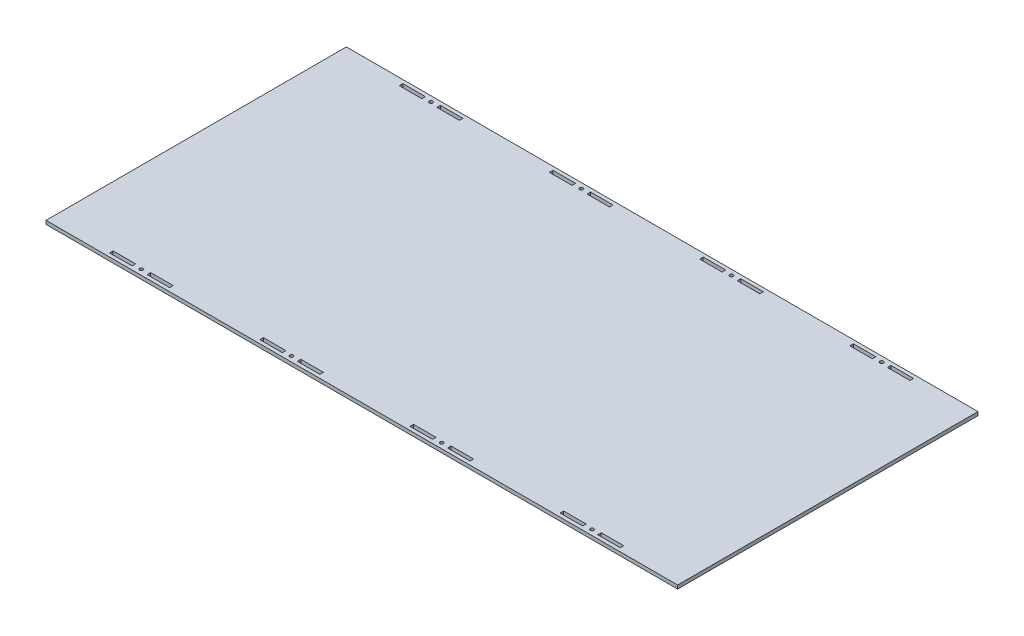
SolidWorks part; units mm, degrees
ref_plane "Front Plane" through (0, 0, 0) normal (0, 0, 1) x (1, 0, 0)
ref_plane "Top Plane" through (0, 0, 0) normal (0, 1, 0) x (1, 0, 0)
ref_plane "Right Plane" through (0, 0, 0) normal (1, 0, 0) x (0, 0, -1)
sketch "Sketch1" plane through (0, 0, 0) normal (0, 1, 0) x (1, 0, 0)
  line L1 (0, 0) -> (534.162, 0)
  line L2 (0, 0) -> (0, 254)
  line L3 (0, 254) -> (534.162, 254)
  line L4 (534.162, 0) -> (534.162, 254)
  dimension "D1" = 254
  dimension "D2" = 534.162
extrude "Boss-Extrude1" add sketch "Sketch1" along normal blind 3
sketch "Sketch2" plane through (0, 3, 0) normal (0, 1, 0) x (1, 0, 0)
  line L0 (69.85, 4.5) -> (82.55, 4.5) construction
  line L1 (50.8, 6) -> (69.85, 6)
  line L2 (50.8, 6) -> (50.8, 3)
  line L3 (50.8, 3) -> (69.85, 3)
  line L4 (69.85, 6) -> (69.85, 3)
  line L5 (82.55, 6) -> (101.6, 6)
  line L6 (82.55, 6) -> (82.55, 3)
  line L7 (82.55, 3) -> (101.6, 3)
  line L8 (101.6, 6) -> (101.6, 3)
  line L9 (76.2, 4.5) -> (76.2, 0) construction
  line L10 (0, 0) -> (534.162, 0) construction
  line L11 (0, 254) -> (0, 0) construction
  line L12 (177.8, 6) -> (196.85, 6)
  line L13 (177.8, 6) -> (177.8, 3)
  line L14 (177.8, 3) -> (196.85, 3)
  line L15 (196.85, 6) -> (196.85, 3)
  line L16 (209.55, 6) -> (209.55, 3)
  line L17 (209.55, 6) -> (228.6, 6)
  line L18 (209.55, 3) -> (228.6, 3)
  line L19 (228.6, 6) -> (228.6, 3)
  line L20 (304.8, 6) -> (323.85, 6)
  line L21 (304.8, 6) -> (304.8, 3)
  line L22 (304.8, 3) -> (323.85, 3)
  line L23 (323.85, 6) -> (323.85, 3)
  line L24 (336.55, 6) -> (336.55, 3)
  line L25 (336.55, 6) -> (355.6, 6)
  line L26 (336.55, 3) -> (355.6, 3)
  line L27 (355.6, 6) -> (355.6, 3)
  line L28 (431.8, 6) -> (450.85, 6)
  line L29 (431.8, 6) -> (431.8, 3)
  line L30 (431.8, 3) -> (450.85, 3)
  line L31 (450.85, 6) -> (450.85, 3)
  line L32 (463.55, 6) -> (463.55, 3)
  line L33 (463.55, 6) -> (482.6, 6)
  line L34 (463.55, 3) -> (482.6, 3)
  line L35 (482.6, 6) -> (482.6, 3)
  line L36 (0, 127) -> (534.162, 127) construction
  line L37 (534.162, 0) -> (534.162, 254) construction
  line L38 (69.85, 249.5) -> (82.55, 249.5) construction
  line L39 (196.85, 249.5) -> (209.55, 249.5) construction
  line L40 (323.85, 249.5) -> (336.55, 249.5) construction
  line L41 (450.85, 249.5) -> (463.55, 249.5) construction
  line L42 (450.85, 4.5) -> (463.55, 4.5) construction
  line L43 (323.85, 4.5) -> (336.55, 4.5) construction
  line L44 (196.85, 4.5) -> (209.55, 4.5) construction
  line L54 (50.8, 251) -> (69.85, 251)
  line L55 (50.8, 248) -> (69.85, 248)
  line L56 (82.55, 251) -> (101.6, 251)
  line L57 (82.55, 248) -> (101.6, 248)
  line L58 (177.8, 251) -> (196.85, 251)
  line L59 (177.8, 248) -> (196.85, 248)
  line L60 (209.55, 251) -> (228.6, 251)
  line L61 (209.55, 248) -> (228.6, 248)
  line L62 (304.8, 251) -> (323.85, 251)
  line L63 (304.8, 248) -> (323.85, 248)
  line L64 (336.55, 251) -> (355.6, 251)
  line L65 (336.55, 248) -> (355.6, 248)
  line L66 (431.8, 251) -> (450.85, 251)
  line L67 (431.8, 248) -> (450.85, 248)
  line L68 (463.55, 251) -> (482.6, 251)
  line L69 (463.55, 248) -> (482.6, 248)
  line L70 (482.6, 248) -> (482.6, 251)
  line L73 (463.55, 248) -> (463.55, 251)
  line L74 (450.85, 248) -> (450.85, 251)
  line L76 (431.8, 248) -> (431.8, 251)
  line L78 (355.6, 248) -> (355.6, 251)
  line L81 (336.55, 248) -> (336.55, 251)
  line L82 (323.85, 248) -> (323.85, 251)
  line L84 (304.8, 248) -> (304.8, 251)
  line L86 (228.6, 248) -> (228.6, 251)
  line L89 (209.55, 248) -> (209.55, 251)
  line L90 (196.85, 248) -> (196.85, 251)
  line L92 (177.8, 248) -> (177.8, 251)
  line L94 (101.6, 248) -> (101.6, 251)
  line L96 (82.55, 248) -> (82.55, 251)
  line L98 (69.85, 248) -> (69.85, 251)
  line L100 (50.8, 248) -> (50.8, 251)
  dimension "D1" = 76.2
  dimension "D2" = 19.05
  dimension "D3" = 19.05
  dimension "D4" = 12.7
  dimension "D5" = 3
  dimension "D6" = 3
  dimension "D7" = 3
  dimension "D8" = 4
extrude "Cut-Extrude1" cut sketch "Sketch2" against normal through all
hole_wizard "#4 Clearance Hole1" positions "Sketch4" profile "Sketch3" hole size "#4" standard "ANSI Inch" end condition through all
sketch "Sketch4" plane through (0, 3, 0) normal (0, 1, 0) x (1, 0, 0)
  line L0 (69.85, 249.5) -> (82.55, 249.5) construction
  line L1 (196.85, 249.5) -> (209.55, 249.5) construction
  line L2 (323.85, 249.5) -> (336.55, 249.5) construction
  line L3 (450.85, 249.5) -> (463.55, 249.5) construction
  line L4 (450.85, 4.5) -> (463.55, 4.5) construction
  line L5 (323.85, 4.5) -> (336.55, 4.5) construction
  line L6 (196.85, 4.5) -> (209.55, 4.5) construction
  line L7 (69.85, 4.5) -> (82.55, 4.5) construction
  point P0 (76.2, 249.5)
  point P2 (203.2, 249.5)
  point P4 (330.2, 249.5)
  point P6 (457.2, 249.5)
  point P8 (457.2, 4.5)
  point P10 (330.2, 4.5)
  point P12 (203.2, 4.5)
  point P14 (76.2, 4.5)
  point P19 (76.2, 249.5)
  point P22 (203.2, 249.5)
  point P25 (330.2, 249.5)
  point P28 (457.2, 249.5)
  point P31 (457.2, 4.5)
  point P34 (330.2, 4.5)
  point P38 (203.2, 4.5)
  point P43 (76.2, 4.5)
sketch "Sketch3" plane through (76.2, 3, -249.5) normal (1, 0, 0) x (0, 0, 1)
  line L0 (0, 0) -> (0, 3)
  line L1 (0, 3) -> (1.4732, 3)
  line L2 (1.4732, 3) -> (1.4732, 0)
  line L5 (1.4732, 0) -> (0, 0)
  line L11 (0, -6.35) -> (0, 107.95) construction
  dimension "Thru Hole Dia." = 2.9464
  dimension "Thru Hole Depth" = 3
